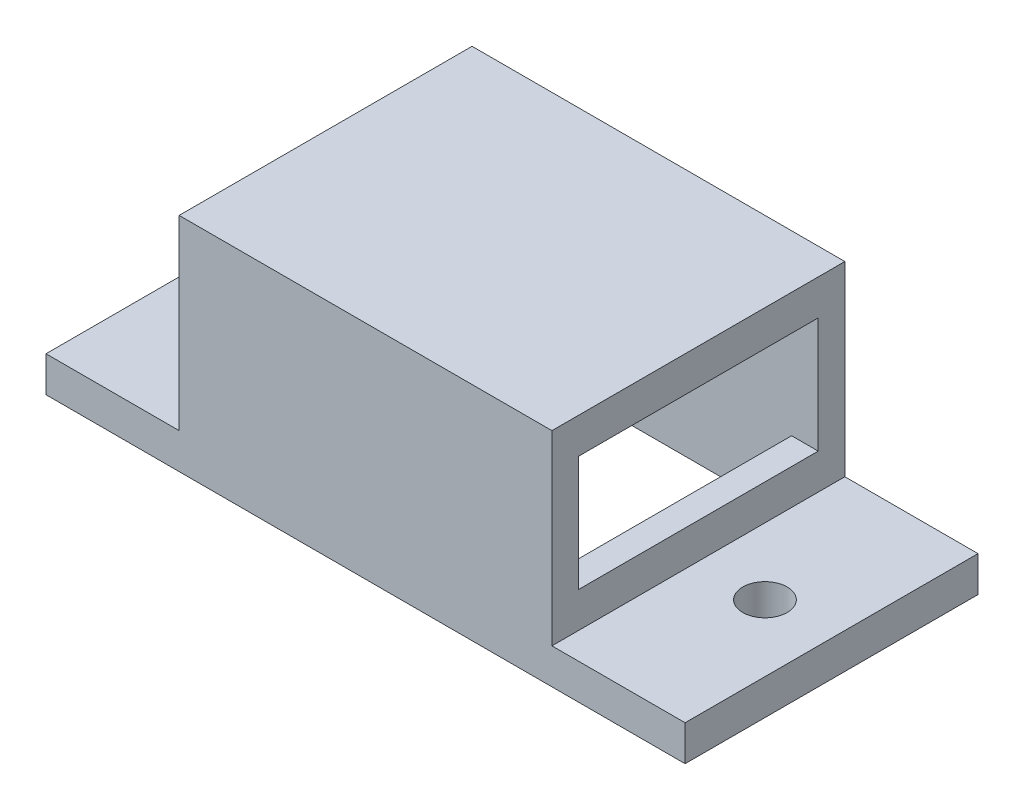
SolidWorks part; units mm, degrees
ref_plane "前基準面" through (0, 0, 0) normal (0, 0, 1) x (1, 0, 0)
ref_plane "上基準面" through (0, 0, 0) normal (0, 1, 0) x (1, 0, 0)
ref_plane "右基準面" through (0, 0, 0) normal (1, 0, 0) x (0, 0, -1)
sketch "草圖1" plane through (0, 0, 0) normal (0, 1, 0) x (1, 0, 0)
  line L1 (-21, 16.5) -> (21, 16.5)
  line L2 (-21, 16.5) -> (-21, -16.5)
  line L3 (-21, -16.5) -> (21, -16.5)
  line L4 (21, 16.5) -> (21, -16.5)
  line L5 (-21, 16.5) -> (21, -16.5) construction
  line L6 (-21, -16.5) -> (21, 16.5) construction
  point P0 (0, 0)
  dimension "D1" = 42
  dimension "D2" = 33
extrude "填料-伸長1" add sketch "草圖1" along normal blind 25
sketch "草圖2" plane through (0, 0, 0) normal (0, 1, 0) x (1, 0, 0)
  line L0 (21, 16.5) -> (-21, 16.5) construction
  line L1 (-36, 16.5) -> (36, 16.5)
  line L2 (-36, 16.5) -> (-36, -16.5)
  line L3 (-36, -16.5) -> (36, -16.5)
  line L4 (36, 16.5) -> (36, -16.5)
  line L5 (-36, 16.5) -> (36, -16.5) construction
  line L6 (-36, -16.5) -> (36, 16.5) construction
  line L7 (-21, 16.5) -> (-21, -16.5) construction
  point P0 (0, 0)
  dimension "D1" = 0
  dimension "D2" = 15
extrude "填料-伸長2" add sketch "草圖2" along normal blind 4
sketch "草圖3" plane through (0, 0, 0) normal (0, -1, 0) x (1, 0, 0)
  line L1 (-18, 13.5) -> (18, 13.5)
  line L2 (-18, 13.5) -> (-18, -13.5)
  line L3 (-18, -13.5) -> (18, -13.5)
  line L4 (18, 13.5) -> (18, -13.5)
  line L5 (-18, 13.5) -> (18, -13.5) construction
  line L6 (-18, -13.5) -> (18, 13.5) construction
  point P0 (0, 0)
  dimension "D1" = 36
  dimension "D2" = 27
extrude "除料-伸長1" cut sketch "草圖3" against normal blind 21
sketch "草圖4" plane through (-21, 0, 0) normal (-1, 0, 0) x (0, 0, 1)
  line L0 (-16.5, 25) -> (16.5, 25) construction
  line L1 (13.5, 8) -> (-13.5, 8)
  line L2 (13.5, 8) -> (13.5, 21)
  line L3 (13.5, 21) -> (-13.5, 21)
  line L4 (-13.5, 8) -> (-13.5, 21)
  line L5 (13.5, 8) -> (-13.5, 21) construction
  line L6 (13.5, 21) -> (-13.5, 8) construction
  line L7 (-16.5, 4) -> (16.5, 4) construction
  line L8 (-16.5, 25) -> (-16.5, 4) construction
  line L9 (16.5, 25) -> (16.5, 4) construction
  point P0 (0, 14.5)
  dimension "D1" = 4
  dimension "D2" = 4
  dimension "D3" = 3
  dimension "D4" = 3
extrude "除料-伸長2" cut sketch "草圖4" against normal through all
sketch "草圖5" plane through (0, 0, 0) normal (0, -1, 0) x (1, 0, 0)
  line L0 (36, 16.5) -> (36, -16.5) construction
  line L1 (0, 0) -> (0, -11.5686)
  circle A0 centre (28.5, 0) radius 2.5
  circle A1 centre (-28.5, 0) radius 2.5
  dimension "D1" = 5
  dimension "D2" = 7.5
extrude "除料-伸長3" cut sketch "草圖5" against normal through all contours A0 | A1
